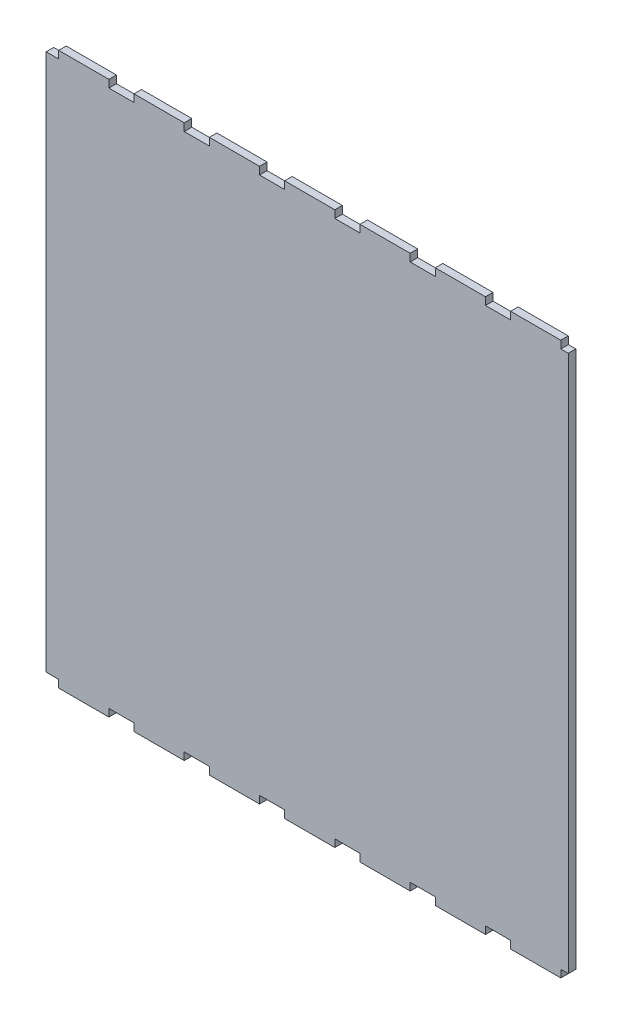
SolidWorks part; units mm, degrees
ref_plane "Plan de face" through (0, 0, 0) normal (0, 0, 1) x (1, 0, 0)
ref_plane "Plan de dessus" through (0, 0, 0) normal (0, 1, 0) x (1, 0, 0)
ref_plane "Plan de droite" through (0, 0, 0) normal (1, 0, 0) x (0, 0, -1)
sketch "Esquisse1" plane through (0, 0, 0) normal (0, 0, 1) x (1, 0, 0)
  line L1 (-104, 110) -> (104, 110)
  line L2 (-104, 110) -> (-104, -110)
  line L3 (-104, -110) -> (104, -110)
  line L4 (104, 110) -> (104, -110)
  line L5 (-104, 110) -> (104, -110) construction
  line L6 (-104, -110) -> (104, 110) construction
  point P0 (0, 0)
  dimension "D1" = 208
  dimension "D2" = 220
extrude "Boss.-Extru.1" add sketch "Esquisse1" along normal blind 3
sketch "Esquisse2" plane through (0, 0, 3) normal (0, 0, 1) x (1, 0, 0)
  line L0 (104, 110) -> (-104, 110) construction
  line L1 (-109, 110) -> (-99, 110)
  line L2 (-109, 110) -> (-109, 107)
  line L3 (-109, 107) -> (-99, 107)
  line L4 (-99, 110) -> (-99, 107)
  line L5 (-104, 110) -> (-104, -110) construction
  line L6 (-79, 110) -> (-79, 107)
  line L7 (-79, 110) -> (-69, 110)
  line L8 (-69, 110) -> (-69, 107)
  line L9 (-79, 107) -> (-69, 107)
  line L10 (-49, 110) -> (-49, 107)
  line L11 (-49, 110) -> (-39, 110)
  line L12 (-39, 110) -> (-39, 107)
  line L13 (-49, 107) -> (-39, 107)
  line L14 (-19, 110) -> (-19, 107)
  line L15 (-19, 110) -> (-9, 110)
  line L16 (-9, 110) -> (-9, 107)
  line L17 (-19, 107) -> (-9, 107)
  line L18 (11, 110) -> (11, 107)
  line L19 (11, 110) -> (21, 110)
  line L20 (21, 110) -> (21, 107)
  line L21 (11, 107) -> (21, 107)
  line L22 (41, 110) -> (41, 107)
  line L23 (41, 110) -> (51, 110)
  line L24 (51, 110) -> (51, 107)
  line L25 (41, 107) -> (51, 107)
  line L26 (71, 110) -> (71, 107)
  line L27 (71, 110) -> (81, 110)
  line L28 (81, 110) -> (81, 107)
  line L29 (71, 107) -> (81, 107)
  line L30 (101, 110) -> (101, 107)
  line L31 (101, 110) -> (111, 110)
  line L32 (111, 110) -> (111, 107)
  line L33 (101, 107) -> (111, 107)
  line L54 (-104, 0) -> (104, 0) construction
  line L55 (104, -110) -> (104, 110) construction
  line L76 (101, -107) -> (111, -107)
  line L77 (111, -110) -> (111, -107)
  line L78 (101, -110) -> (111, -110)
  line L79 (101, -110) -> (101, -107)
  line L80 (71, -107) -> (81, -107)
  line L81 (81, -110) -> (81, -107)
  line L82 (71, -110) -> (81, -110)
  line L83 (71, -110) -> (71, -107)
  line L84 (41, -107) -> (51, -107)
  line L85 (51, -110) -> (51, -107)
  line L86 (41, -110) -> (51, -110)
  line L87 (41, -110) -> (41, -107)
  line L88 (11, -107) -> (21, -107)
  line L89 (21, -110) -> (21, -107)
  line L90 (11, -110) -> (21, -110)
  line L91 (11, -110) -> (11, -107)
  line L92 (-19, -107) -> (-9, -107)
  line L93 (-9, -110) -> (-9, -107)
  line L94 (-19, -110) -> (-9, -110)
  line L95 (-19, -110) -> (-19, -107)
  line L96 (-49, -107) -> (-39, -107)
  line L97 (-39, -110) -> (-39, -107)
  line L98 (-49, -110) -> (-39, -110)
  line L99 (-49, -110) -> (-49, -107)
  line L100 (-79, -107) -> (-69, -107)
  line L101 (-69, -110) -> (-69, -107)
  line L102 (-79, -110) -> (-69, -110)
  line L103 (-79, -110) -> (-79, -107)
  line L104 (-99, -110) -> (-99, -107)
  line L105 (-109, -107) -> (-99, -107)
  line L106 (-109, -110) -> (-109, -107)
  line L107 (-109, -110) -> (-99, -110)
  dimension "D1" = 10
  dimension "D2" = 3
  dimension "D3" = 5
  dimension "D5" = 20
  dimension "D4" = 8
extrude "Enlèv. mat.-Extru.1" cut sketch "Esquisse2" against normal blind 3
